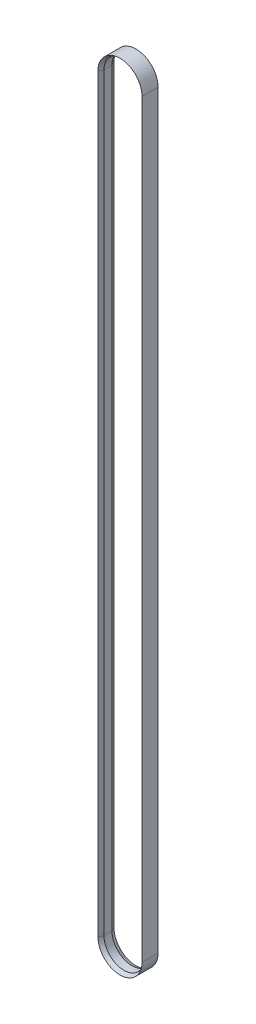
SolidWorks part; units mm, degrees
material "Silicon Rubber"
ref_plane "Front Plane" through (0, 0, 0) normal (0, 0, 1) x (1, 0, 0)
ref_plane "Top Plane" through (0, 0, 0) normal (0, 1, 0) x (1, 0, 0)
ref_plane "Right Plane" through (0, 0, 0) normal (1, 0, 0) x (0, 0, -1)
sketch "Sketch2" plane through (0, 0, 0) normal (0, 0, 1) x (1, 0, 0)
  line L0 (0, 0) -> (1, 0) construction
  line L1 (0, 0) -> (0, 1) construction
  line L2 (25, 0) -> (25, -935.5)
  line L3 (-25, -935.5) -> (-25, 0)
  arc A0 (-25, 0) -> (25, 0) centre (0, 0) cw
  arc A1 (25, -935.5) -> (-25, -935.5) centre (0, -935.5) cw
ref_plane "Plane1" through (0, 0, 0) normal (0, 1, 0) x (1, 0, 0)
sketch "Sketch3" plane through (0, 0, 0) normal (0, 1, 0) x (1, 0, 0)
  line L0 (25, 5) -> (25, -5)
  line L1 (25, -5) -> (27.5, -10)
  line L2 (27.5, -10) -> (27.5, 10)
  line L3 (27.5, 10) -> (25, 5)
  line L4 (-25, 0) -> (25, 0) construction
  dimension "D1" = 10
  dimension "D2" = 25
  dimension "D3" = 5
  dimension "D4" = 20
  dimension "D5" = 10
  dimension "D6" = 2.5
sweep "Sweep1" add profiles "Sketch3" path "Sketch2"
